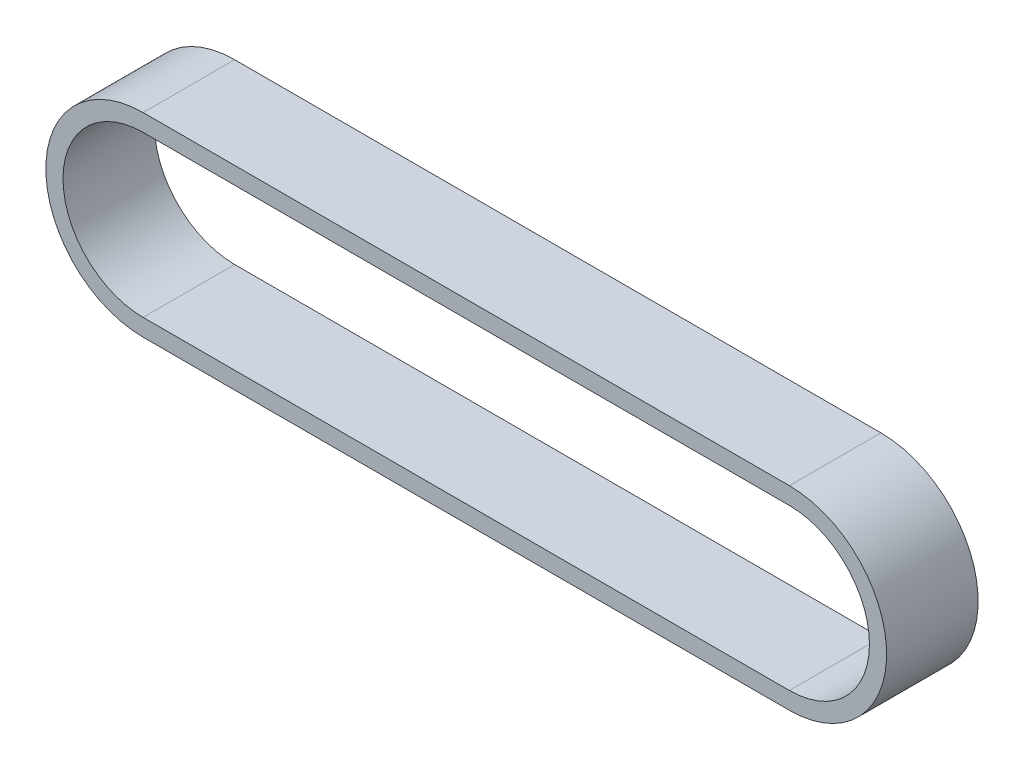
SolidWorks part; units mm, degrees
material "PF"
ref_plane "Piano frontale" through (0, 0, 0) normal (0, 0, 1) x (1, 0, 0)
ref_plane "Piano superiore" through (0, 0, 0) normal (0, 1, 0) x (1, 0, 0)
ref_plane "Piano destro" through (0, 0, 0) normal (1, 0, 0) x (0, 0, -1)
sketch "Schizzo1"
  line L0 (0, 0) -> (-45.1774, 0) construction
  line L1 (0, -5.6) -> (-45.1774, -5.6)
  line L2 (0, 5.6) -> (-45.1774, 5.6)
  line L3 (0, 0) -> (-45.1774, 0) construction
  line L4 (0, -6.8) -> (-45.1774, -6.8)
  line L5 (0, 6.8) -> (-45.1774, 6.8)
  arc A0 (0, -5.6) -> (0, 5.6) centre (0, 0) ccw
  arc A1 (-45.1774, 5.6) -> (-45.1774, -5.6) centre (-45.1774, 0) ccw
  arc A2 (0, -6.8) -> (0, 6.8) centre (0, 0) ccw
  arc A3 (-45.1774, 6.8) -> (-45.1774, -6.8) centre (-45.1774, 0) ccw
  point P3 (-22.5887, 0)
  point P8 (-22.5887, 0)
  line B0 (0, 0) -> (-45.1774, 0) construction
  dimension "D2" = 5.6
  dimension "D1" = 1.2
sketch_block_instance "puleggia piccola-1"
sketch_block "puleggia piccola"
extrude "Estrusione-Estrusione2" add sketch "Schizzo1" along normal blind 6.4
